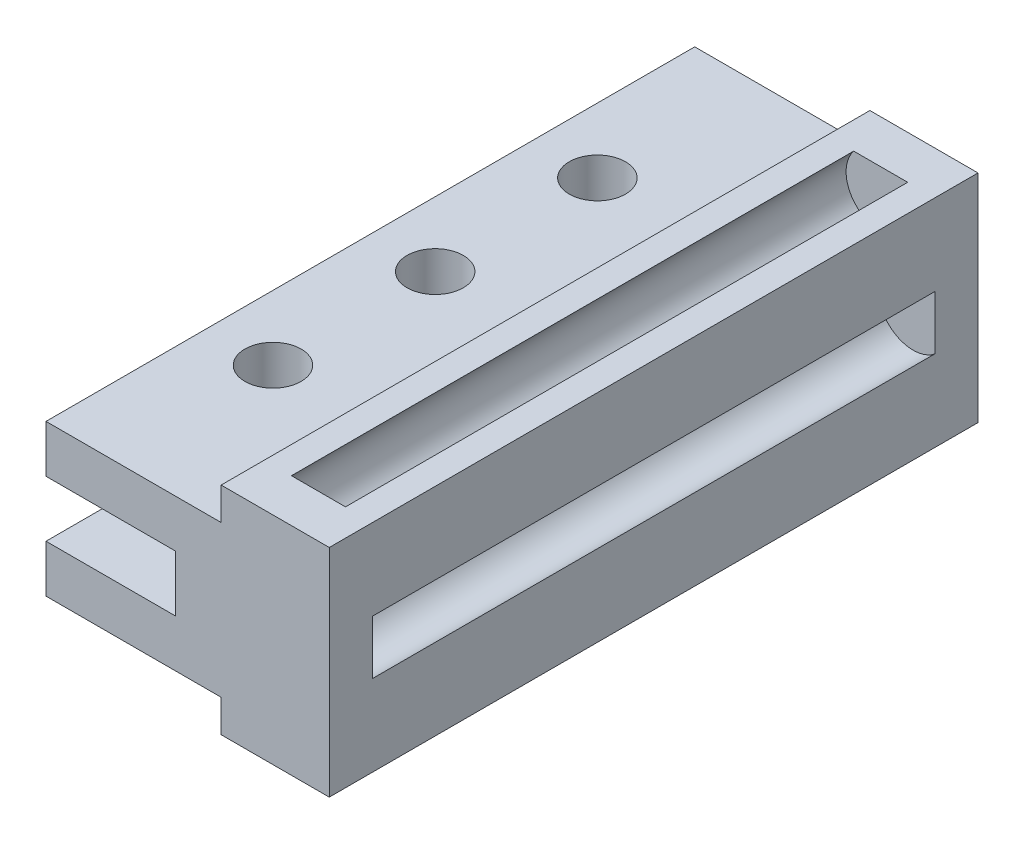
SolidWorks part; units mm, degrees
ref_plane "前视基准面" through (0, 0, 0) normal (0, 0, 1) x (1, 0, 0)
ref_plane "上视基准面" through (0, 0, 0) normal (0, 1, 0) x (1, 0, 0)
ref_plane "右视基准面" through (0, 0, 0) normal (1, 0, 0) x (0, 0, -1)
sketch "草图1" plane through (0, 0, 0) normal (0, 0, 1) x (1, 0, 0)
  line L0 (-2.1, 3.5) -> (0, 3.5)
  line L1 (5, 5) -> (3.749, 5)
  line L3 (5, -5) -> (3.749, -5)
  line L4 (5, 5) -> (5, 1.249)
  line L5 (0, -3.5) -> (-2.1, -3.5)
  line L6 (-8.1, 3.5) -> (-8.1, 1.3)
  line L7 (1.251, 5) -> (0, 5)
  line L8 (0, 5) -> (0, 3.5)
  line L10 (5, -1.249) -> (5, -5)
  line L11 (-2.1, 3.5) -> (-8.1, 3.5)
  line L13 (-8.1, -3.5) -> (-2.1, -3.5)
  line L16 (-8.1, 1.3) -> (-2.1, 1.3)
  line L18 (-8.1, -1.3) -> (-2.1, -1.3)
  line L19 (2.5, 5) -> (2.5, 4) construction
  line L20 (2.5, -5) -> (2.5, -4) construction
  line L21 (5, 0) -> (4, 0) construction
  line L23 (1.251, -5) -> (0, -5)
  line L24 (0, -5) -> (0, -3.5)
  line L25 (-2.1, 1.3) -> (-2.1, -1.3)
  line L26 (-8.1, -1.3) -> (-8.1, -3.5)
  arc A0 (3.749, 5) -> (1.251, 5) centre (2.5, 4) cw
  arc A1 (5, -1.249) -> (5, 1.249) centre (4, 0) cw
  arc A2 (1.251, -5) -> (3.7433, -5.007) centre (2.5, -4) cw
extrude "凸台-拉伸1" add sketch "草图1" along normal blind 30 contours L23 A2 L3 L10 A1 L4 L1 A0 L7 L8 L0 L11 L6 L16 L25 L18 L26 L13 L5 L24
sketch "草图2" plane through (0, -3.5, 0) normal (0, -1, 0) x (1, 0, 0)
  line L0 (-8.1, 0) -> (-2.0999, 0) construction
  line L1 (-8.1, 0) -> (0, 0) construction
  line L2 (-5.0999, 0) -> (-5.0999, 15.0027) construction
  line L3 (-5.0999, 15.0027) -> (-5.0999, 30.0027) construction
  circle A0 centre (-5.0999, 15.0027) radius 1.3
  circle A1 centre (-5.0999, 7.5014) radius 1.3
  circle A2 centre (-5.0999, 22.5027) radius 1.3
extrude "切除-拉伸1" cut sketch "草图2" against normal blind 30
sketch "草图3" plane through (0, 0, 30) normal (0, 0, 1) x (1, 0, 0)
  line L0 (0, -5) -> (0, 5)
  line L1 (0, 5) -> (5, 5)
  line L2 (5, 5) -> (5, -5)
  line L3 (5, -5) -> (0, -5)
extrude "凸台-拉伸2" add sketch "草图3" against normal blind 2
sketch "草图4" plane through (0, 0, 0) normal (0, 0, -1) x (-1, 0, 0)
  line L0 (0, 5) -> (0, -5)
  line L1 (0, -5) -> (-5, -5)
  line L2 (-5, -5) -> (-5, 5)
  line L4 (-1.251, 5) -> (-3.749, 5)
  line L19 (-1.251, -5) -> (0, -5)
  line L20 (0, -5) -> (0, -3.5)
  line L21 (0, -3.5) -> (8.1, -3.5)
  line L22 (8.1, -3.5) -> (8.1, -1.3)
  line L23 (8.1, -1.3) -> (2.1, -1.3)
  line L24 (2.1, -1.3) -> (2.1, 1.3)
  line L25 (2.1, 1.3) -> (8.1, 1.3)
  line L26 (8.1, 1.3) -> (8.1, 3.5)
  line L27 (8.1, 3.5) -> (0, 3.5)
  line L28 (0, 3.5) -> (0, 5)
  line L29 (0, 5) -> (-1.251, 5)
  line L30 (-3.749, 5) -> (-5, 5)
  line L31 (-5, 5) -> (-5, 1.249)
  line L32 (-5, -1.249) -> (-5, -5)
  line L33 (-5, -5) -> (-3.749, -5)
  line L35 (0, 3.5) -> (0, 5)
  line L44 (0, 5) -> (-1.251, 5)
  line L45 (-3.749, 5) -> (-5, 5)
  arc A3 (-3.749, 5) -> (-1.251, 5) centre (-2.5, 4) ccw
  arc A4 (-5, -1.249) -> (-5, 1.249) centre (-4, 0) ccw
  arc A5 (-1.251, -5) -> (-3.749, -5) centre (-2.5, -4) ccw
  line M1 (-1.251, -5) -> (0, -5)
  line M10 (0, -5) -> (0, -3.5)
  line M11 (0, 5) -> (-1.251, 5)
  arc M12 (-1.251, 5) -> (-3.749, 5) centre (-2.5, 4) cw
  line M13 (-3.749, 5) -> (-5, 5)
  line M14 (-5, 5) -> (-5, 1.249)
  arc M15 (-5, 1.249) -> (-5, -1.249) centre (-4, 0) cw
  line M16 (-5, -1.249) -> (-5, -5)
  line M17 (-5, -5) -> (-3.749, -5)
  arc M18 (-3.749, -5) -> (-1.251, -5) centre (-2.5, -4) cw
  line M41 (0, 3.5) -> (0, 5)
  dimension "D1" = 0
extrude "凸台-拉伸3" add sketch "草图4" against normal blind 2 contours L0 M41 M11 M12 M13 M14 M15 M16 M17 M18 M1 M10 | L4 M12 | L2 M15 | L1 M18
